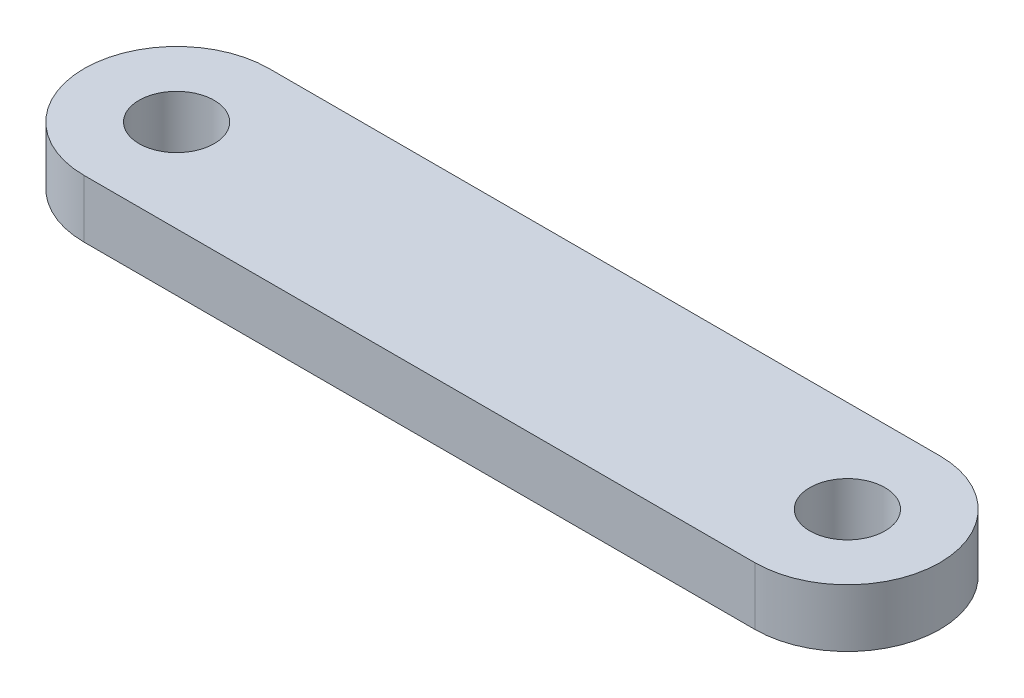
SolidWorks part; units mm, degrees
ref_plane "Front Plane" through (0, 0, 0) normal (0, 0, 1) x (1, 0, 0)
ref_plane "Top Plane" through (0, 0, 0) normal (0, 1, 0) x (1, 0, 0)
ref_plane "Right Plane" through (0, 0, 0) normal (1, 0, 0) x (0, 0, -1)
sketch "Sketch1" plane through (0, 0, 0) normal (0, 1, 0) x (1, 0, 0)
  line L0 (0, 0) -> (29, 0) construction
  line L1 (0, 4) -> (29, 4)
  line L2 (0, -4) -> (29, -4)
  arc A0 (0, 4) -> (0, -4) centre (0, 0) ccw
  arc A1 (29, -4) -> (29, 4) centre (29, 0) ccw
  point P3 (14.5, 0)
  dimension "D2" = 4
  dimension "D1" = 29
extrude "Boss-Extrude1" add sketch "Sketch1" along normal blind 2.5
sketch "Sketch2" plane through (0, 2.5, 0) normal (0, 1, 0) x (1, 0, 0)
  circle A0 centre (0, 0) radius 1.625
  circle A1 centre (29, 0) radius 1.625
  dimension "D1" = 3.25
  dimension "D2" = 3.25
  dimension "D3" = 29
extrude "Cut-Extrude1" cut sketch "Sketch2" against normal up to surface (2.5 mm away) up to face at (14.5, 0, 0)
